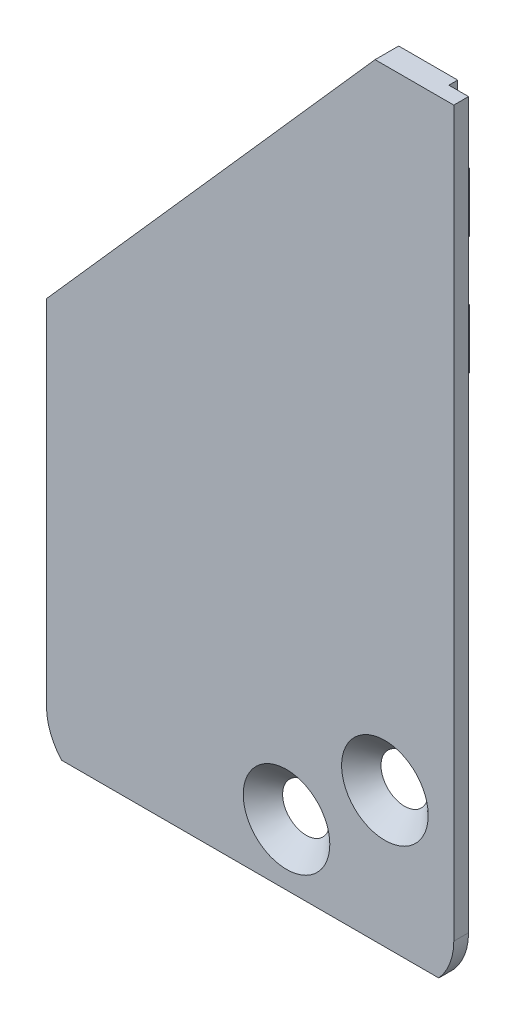
SolidWorks part; units mm, degrees
ref_plane "Front Plane" through (0, 0, 0) normal (0, 0, 1) x (1, 0, 0)
ref_plane "Top Plane" through (0, 0, 0) normal (0, 1, 0) x (1, 0, 0)
ref_plane "Right Plane" through (0, 0, 0) normal (1, 0, 0) x (0, 0, -1)
sketch "Sketch1" plane through (0, 0, 0) normal (0, 0, 1) x (1, 0, 0)
  line L10 (11.2551, 53.7336) -> (13.2551, 53.7336)
  line L11 (13.2551, 50.7336) -> (11.2551, 50.7336)
  line L12 (11.2551, 47.7336) -> (13.2551, 47.7336)
  line L13 (13.2551, 44.7336) -> (11.2551, 44.7336)
  line L14 (13.2551, 53.7336) -> (13.2551, 50.7336)
  line L15 (13.2551, 47.7336) -> (13.2551, 44.7336)
  line L26 (13.2551, 19.1086) -> (13.2551, 33.2336)
  line L27 (-5.4449, 19.1086) -> (13.2551, 19.1086)
  line L28 (-3.4449, 20.6193) -> (13.2551, 33.2336)
  line L29 (-3.4449, 20.6193) -> (-5.4449, 19.1086)
  arc A2 (11.2551, 53.7336) -> (11.2551, 50.7336) centre (11.2551, 52.2336) ccw
  arc A3 (11.2551, 47.7336) -> (11.2551, 44.7336) centre (11.2551, 46.2336) ccw
extrude "Boss-Extrude1" add sketch "Sketch1" along a picked direction on the side against the normal blind 0.8 contours L10 A2 L11 L14 | L12 A3 L13 L15
sketch "Sketch2" plane through (0, 0, 0) normal (0, 0, 1) x (1, 0, 0)
  line L0 (-3.4449, 19.1086) -> (11.2551, 19.1086) construction
  line L1 (-5.4449, 19.1086) -> (13.2551, 19.1086)
  line L25 (-5.4449, 21.1086) -> (-5.4449, 40.1685) construction
  line L26 (13.2551, 57.9086) -> (13.2551, 21.1086) construction
  line L27 (10.2551, 57.9086) -> (-5.4449, 40.1685) construction
  line L28 (13.2551, 57.9086) -> (10.2551, 57.9086) construction
  line L29 (-5.4449, 19.1086) -> (-5.4449, 40.1685)
  line L30 (13.2551, 57.9086) -> (13.2551, 19.1086)
  line L31 (10.2551, 57.9086) -> (-5.4449, 40.1685)
  line L32 (13.2551, 57.9086) -> (10.2551, 57.9086)
extrude "Boss-Extrude3" add sketch "Sketch2" along normal up to vertex (1 mm away) and the other way blind 0.2
fillet "Fillet1" radius 2 2 edges at (13.2551, 19.1086, 0.4) (-5.4449, 19.1086, 0.4)
ref_plane "Plane1" through (0, 0, 0) normal (0, 0, -1) x (-1, 0, 0)
sketch "Sketch3" plane through (0, 0, 0) normal (0, 0, -1) x (-1, 0, 0)
  line L4 (-13.2551, 33.2336) -> (-13.2551, 19.1086)
  line L5 (3.4449, 20.6193) -> (-13.2551, 33.2336)
  line L6 (5.4449, 19.1086) -> (3.4449, 20.6193)
  line L7 (-13.2551, 19.1086) -> (5.4449, 19.1086)
  line L8 (-13.2551, 33.2336) -> (-13.2551, 19.1086)
  line L9 (3.4449, 20.6193) -> (-13.2551, 33.2336)
  line L10 (5.4449, 19.1086) -> (3.4449, 20.6193)
  line L11 (-13.2551, 19.1086) -> (5.4449, 19.1086)
  dimension "D1" = 0
extrude "Cut-Extrude1" cut sketch "Sketch3" along normal blind 0.2
sketch "Sketch4" plane through (0, 0, 1) normal (0, 0, 1) x (1, 0, 0)
  line L8 (-6.4449, 40.1685) -> (-6.4449, 21.1086)
  line L9 (-6.4449, 39.0385) -> (-6.4449, 21.1086)
  line L11 (-5.681, 19.1086) -> (13.4911, 19.1086)
  line L12 (14.2551, 21.1086) -> (14.2551, 57.9086)
  line L13 (14.2551, 21.1086) -> (14.2551, 57.9086)
  line L14 (-3.4449, 19.1086) -> (11.2551, 19.1086) construction
  line L17 (13.2551, 57.9086) -> (10.2551, 57.9086) construction
  line L18 (10.2551, 57.9086) -> (-5.4449, 40.1685) construction
  line L19 (14.2551, 57.9086) -> (10.2551, 57.9086)
  line L20 (10.2551, 57.9086) -> (-6.4449, 39.0385)
  arc A2 (-6.4449, 21.1086) -> (-3.4449, 18.1086) centre (-3.4449, 21.1086) ccw
  arc A3 (-6.4449, 21.1086) -> (-5.681, 19.1086) centre (-3.4449, 21.1086) ccw
  arc A5 (11.2551, 18.1086) -> (14.2551, 21.1086) centre (11.2551, 21.1086) ccw
  arc A6 (13.4911, 19.1086) -> (14.2551, 21.1086) centre (11.2551, 21.1086) ccw
  dimension "D1" = 1
  dimension "D2" = 1
extrude "Boss-Extrude4" add sketch "Sketch4" against normal blind 0.75
hole_wizard "CSK for M2 Flat Head Machine Screw1" positions "Sketch5" profile "Sketch6" countersink size "M2" standard "ANSI Metric"
sketch "Sketch5" plane through (-1.0949, -30.3706, 1) normal (0, 0, 1) x (1, 0, 0)
  line L0 (11.85, 56.3676) -> (6.85, 52.5909) construction
  point P0 (11.85, 56.3676)
  point P2 (6.85, 52.5909)
sketch "Sketch6" plane through (10.7551, 25.997, 1) normal (1, 0, 0) x (0, -1, 0)
  line L0 (0, 0) -> (0, 4.721)
  line L1 (0, 4.721) -> (1.2, 4)
  line L2 (1.2, 4) -> (1.2, 1)
  line L3 (1.2, 1) -> (2.2, 0)
  line L4 (2.2, 0) -> (0, 0)
  line L5 (-1.2, 1) -> (-2.2, 0) construction
  line L6 (0, 4.721) -> (-1.2, 4) construction
  line L7 (0, -6.35) -> (0, 107.95) construction
  dimension "Hole Dia." = 2.4
  dimension "Hole Depth" = 4
  dimension "Near C'Sink Dia." = 4.4
  dimension "Near C'Sink Angle" = 90
  dimension "Drill Angle" = 118
